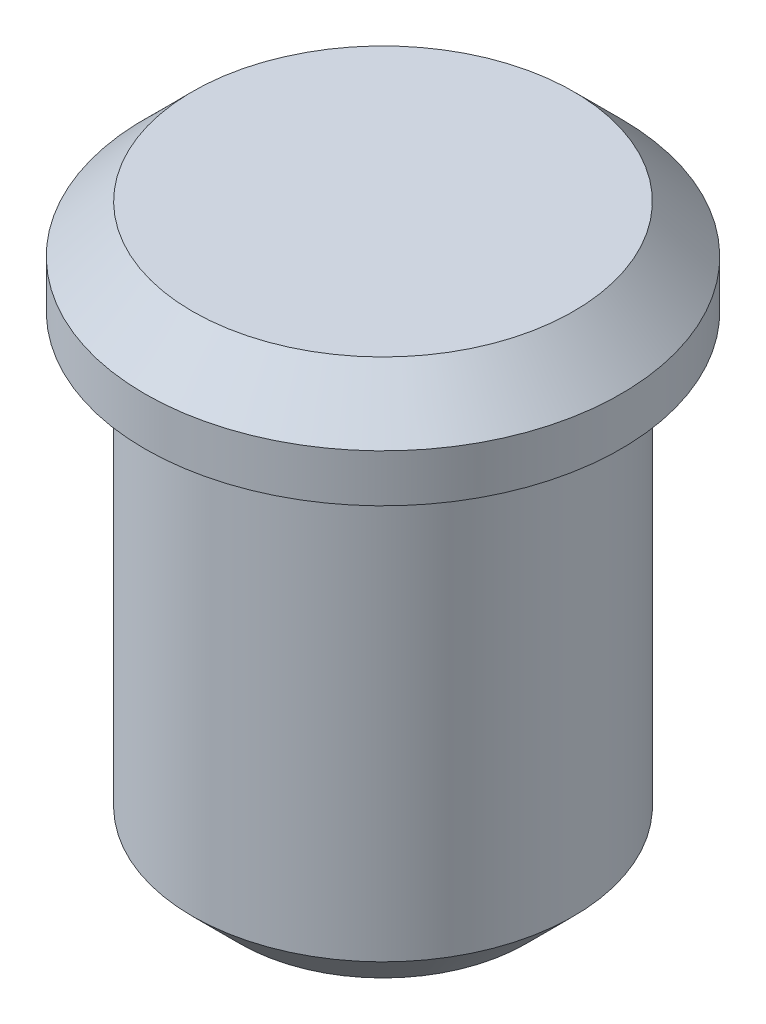
SolidWorks part; units mm, degrees
ref_plane "Plano frontal" through (0, 0, 0) normal (0, 0, 1) x (1, 0, 0)
ref_plane "Plano superior" through (0, 0, 0) normal (0, 1, 0) x (1, 0, 0)
ref_plane "Plano direito" through (0, 0, 0) normal (1, 0, 0) x (0, 0, -1)
sketch "Esboço1" plane through (0, 0, 0) normal (0, 1, 0) x (1, 0, 0)
  circle A0 centre (0, 0) radius 4
  dimension "D1" = 8
extrude "Extrusão1" add sketch "Esboço1" against normal blind 10
sketch "Esboço2" plane through (0, 0, 0) normal (0, 1, 0) x (1, 0, 0)
  circle A0 centre (0, 0) radius 5
  dimension "D1" = 10
extrude "Extrusão2" add sketch "Esboço2" along normal blind 2
chamfer "Chanfro1" distance 1 angle 45 1 edges at (0, -10, 4)
chamfer "Chanfro2" distance 1 angle 45 1 edges at (0, 2, 5)
